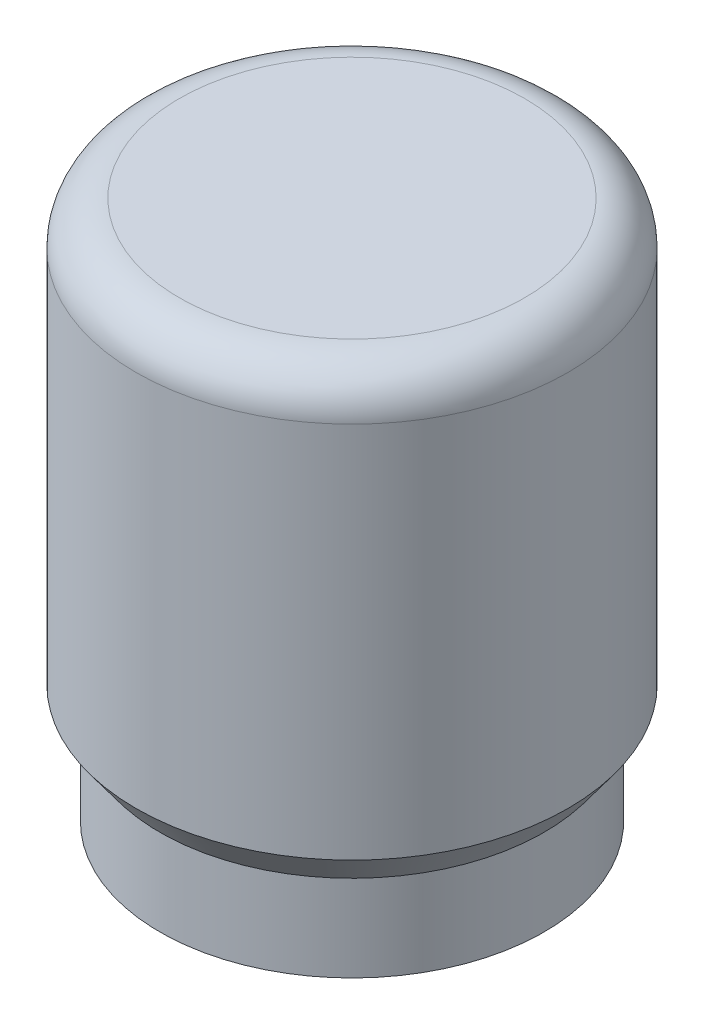
SolidWorks part; units mm, degrees
ref_plane "Front Plane" through (0, 0, 0) normal (0, 0, 1) x (1, 0, 0)
ref_plane "Top Plane" through (0, 0, 0) normal (0, 1, 0) x (1, 0, 0)
ref_plane "Right Plane" through (0, 0, 0) normal (1, 0, 0) x (0, 0, -1)
sketch "Sketch1" plane through (0, 0, 0) normal (0, 0, 1) x (1, 0, 0)
  line L0 (0, 0) -> (0, 41.0076) construction
  line L1 (3, 3.9878) -> (3, 12.954)
  line L2 (3, 12.954) -> (0, 14.6861)
  line L3 (0, 14.6861) -> (0, 15.875)
  line L4 (0, 15.875) -> (5.08, 15.875)
  line L5 (6.35, 14.605) -> (6.35, 3.4958)
  line L6 (6.35, 3.4958) -> (5.6515, 2.54)
  line L7 (5.6515, 2.54) -> (5.6515, 0)
  line L8 (5.6515, 0) -> (4.7625, 0)
  line L9 (4.7625, 0) -> (4.7625, 3.9878)
  line L10 (4.7625, 3.9878) -> (3, 3.9878)
  arc A0 (5.08, 15.875) -> (6.35, 14.605) centre (5.08, 14.605) cw
  dimension "D11" = 1.27
  dimension "D1" = 6
  dimension "D2" = 12.954
  dimension "D3" = 15.875
  dimension "D4" = 12.7
  dimension "D5" = 11.303
  dimension "D6" = 2.54
  dimension "D7" = 36.158
  dimension "D8" = 60
  dimension "D9" = 9.525
  dimension "D10" = 3.9878
revolve "Revolve1" add sketch "Sketch1" angle 360 about L0
sketch "Sketch2" plane through (0, 0, 0) normal (0, 0, 1) x (1, 0, 0)
  circle A0 centre (0, 7.239) radius 1.7272
  dimension "D2" = 3.4544
  dimension "D1" = 7.239
extrude "Cut-Extrude1" cut sketch "Sketch2" against normal through all
